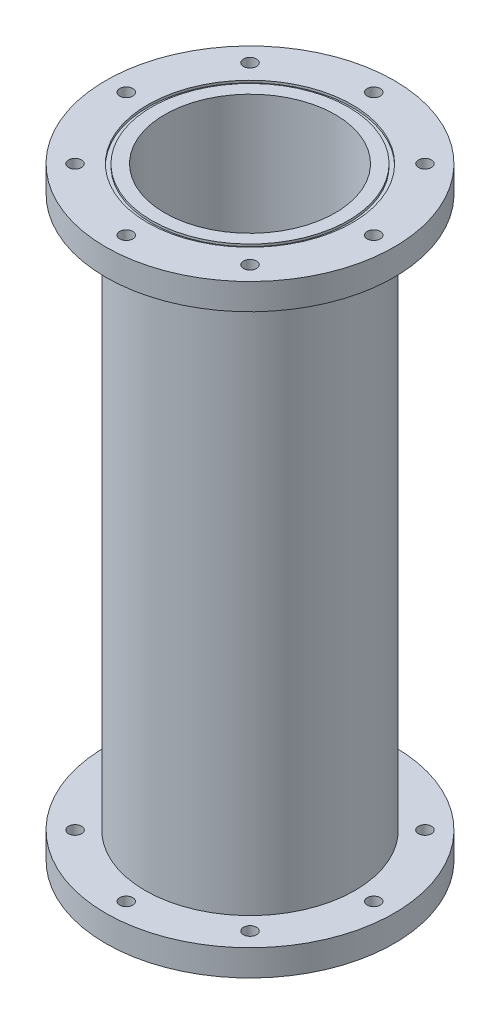
SolidWorks part; units mm, degrees
ref_plane "Front Plane" through (0, 0, 0) normal (0, 0, 1) x (1, 0, 0)
ref_plane "Top Plane" through (0, 0, 0) normal (0, 1, 0) x (1, 0, 0)
ref_plane "Right Plane" through (0, 0, 0) normal (1, 0, 0) x (0, 0, -1)
sketch "Sketch2" plane through (0, 0, 0) normal (0, 1, 0) x (1, 0, 0)
  circle A0 centre (0, 0) radius 41.275
  circle A1 centre (0, 0) radius 50.8
  dimension "D1" = 101.6
  dimension "D2" = 82.55
extrude "Base Cylinder" add sketch "Sketch2" along normal blind 292.1
sketch "Sketch3" plane through (0, 0, 0) normal (0, -1, 0) x (1, 0, 0)
  circle A0 centre (0, 0) radius 41.275
  circle A1 centre (0, 0) radius 69.85
  dimension "D1" = 139.7
extrude "Aft Flange" add sketch "Sketch3" against normal blind 12.7
sketch "Sketch4" plane through (0, 292.1, 0) normal (0, 1, 0) x (1, 0, 0)
  circle A0 centre (0, 0) radius 41.275
  circle A1 centre (0, 0) radius 69.85
extrude "Forward Flange" add sketch "Sketch4" against normal blind 12.7
sketch "Sketch6" plane through (0, 0, 0) normal (0, -1, 0) x (1, 0, 0)
  circle A0 centre (0, 0) radius 49.53
  circle A1 centre (0, 0) radius 47.625
  dimension "D1" = 99.06
  dimension "D2" = 95.25
extrude "O-Ring Slot 1" cut sketch "Sketch6" against normal blind 1.1176
sketch "Sketch7" plane through (0, 292.1, 0) normal (0, 1, 0) x (1, 0, 0)
  circle A0 centre (0, 0) radius 49.53
  circle A1 centre (0, 0) radius 47.625
  dimension "D1" = 99.06
  dimension "D2" = 95.25
extrude "O-Ring Slot 2" cut sketch "Sketch7" against normal blind 1.1176
sketch "Sketch8" plane through (0, 0, 0) normal (0, -1, 0) x (1, 0, 0)
  circle A0 centre (-59.9186, 0) radius 3.175
  circle A1 centre (-42.3688, 42.3688) radius 3.175
  circle A2 centre (0, 59.9186) radius 3.175
  circle A3 centre (42.3688, 42.3688) radius 3.175
  circle A4 centre (59.9186, 0) radius 3.175
  circle A5 centre (42.3688, -42.3688) radius 3.175
  circle A6 centre (0, -59.9186) radius 3.175
  circle A7 centre (-42.3688, -42.3688) radius 3.175
  point P36 (0, 0)
  dimension "D2" = 6.35
  dimension "D1" = 59.9186
  dimension "D3" = 8
extrude "Cut-Extrude4" cut sketch "Sketch8" against normal through all both and the other way through all
